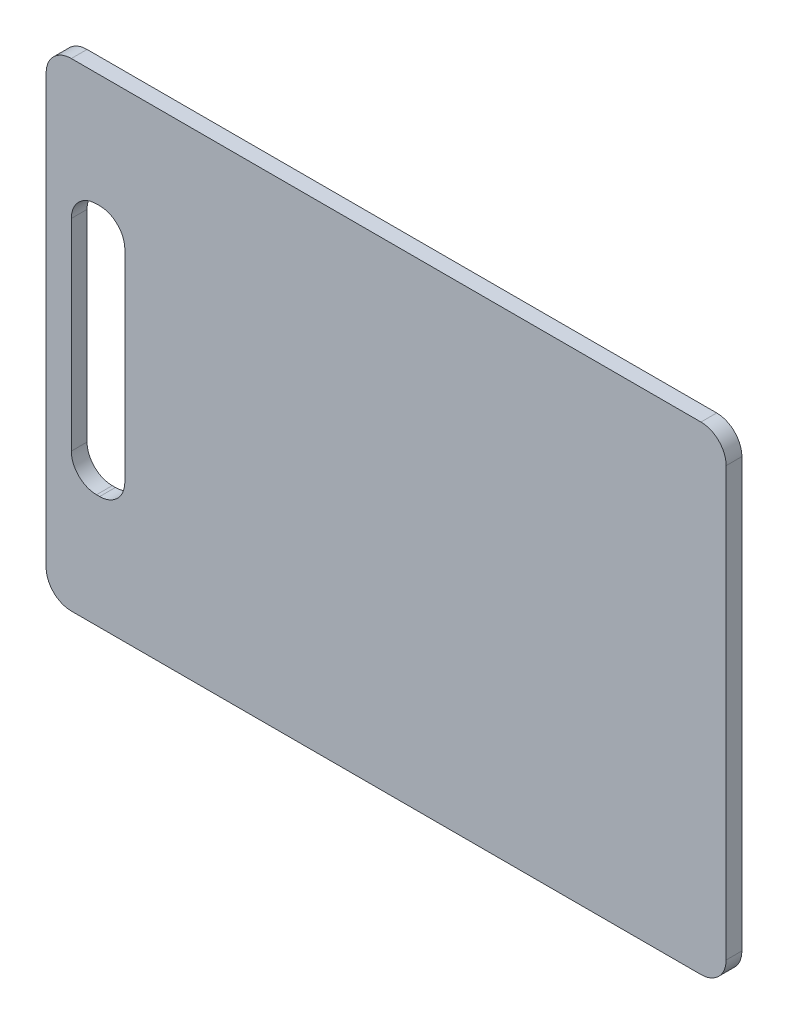
SolidWorks part; units mm, degrees
ref_plane "Front Plane" through (0, 0, 0) normal (0, 0, 1) x (1, 0, 0)
ref_plane "Top Plane" through (0, 0, 0) normal (0, 1, 0) x (1, 0, 0)
ref_plane "Right Plane" through (0, 0, 0) normal (1, 0, 0) x (0, 0, -1)
sketch "Sketch1" plane through (0, 0, 0) normal (0, 0, 1) x (1, 0, 0)
  line L1 (-342.9, 241.3) -> (0, 241.3)
  line L2 (-342.9, 241.3) -> (-342.9, 0)
  line L3 (-342.9, 0) -> (0, 0)
  line L4 (0, 241.3) -> (0, 0)
  line L5 (-330.2, 184.15) -> (-303.2125, 184.15)
  line L6 (-330.2, 184.15) -> (-330.2, 57.15)
  line L7 (-330.2, 57.15) -> (-303.2125, 57.15)
  line L8 (-303.2125, 184.15) -> (-303.2125, 57.15)
  dimension "D1" = 241.3
  dimension "D2" = 342.9
  dimension "D3" = 12.7
  dimension "D4" = 39.6875
  dimension "D5" = 57.15
  dimension "D6" = 184.15
extrude "Boss-Extrude1" add sketch "Sketch1" along normal blind 7.9375
fillet "Fillet1" radius 12.7 8 edges at (-330.2, 57.15, 3.9688) (-303.2125, 57.15, 3.9688) (-303.2125, 184.15, 3.9688) (-330.2, 184.15, 3.9688) (-342.9, 0, 3.9688) (0, 0, 3.9688) (0, 241.3, 3.9688) (-342.9, 241.3, 3.9688)
